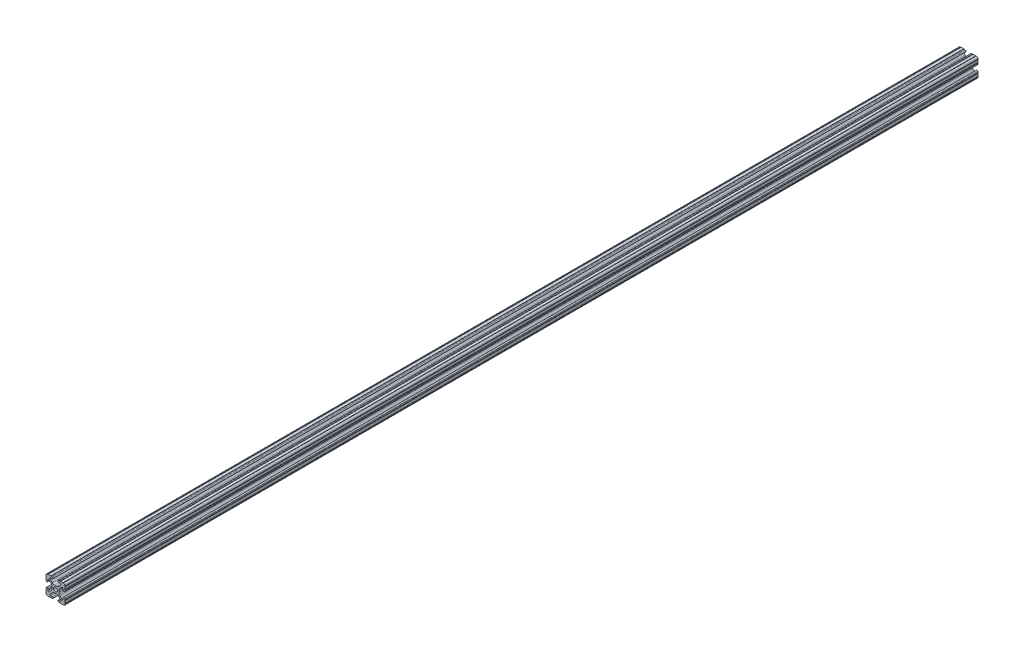
SolidWorks part; units mm, degrees
ref_plane "Front Plane" through (0, 0, 0) normal (0, 0, 1) x (1, 0, 0)
ref_plane "Top Plane" through (0, 0, 0) normal (0, 1, 0) x (1, 0, 0)
ref_plane "Right Plane" through (0, 0, 0) normal (1, 0, 0) x (0, 0, -1)
sketch "Sketch1" plane through (0, 0, 0) normal (0, 0, 1) x (1, 0, 0)
  line L0 (0, 12.7) -> (-12.7814, 12.7) construction
  line L1 (-4.5085, 0) -> (-4.5085, 2.9459)
  line L2 (-6.0437, 12.5461) -> (-10.0976, 12.6876) construction
  line L3 (-11.5616, 12.4229) -> (-4.3159, 12.1699) construction
  line L4 (-6.4364, 10.3486) -> (-6.3592, 12.5571) construction
  line L6 (-2.9459, 4.5085) -> (0, 4.5085)
  line L7 (0, 0) -> (0, 12.7) construction
  line L8 (0, 0) -> (-12.7814, 0) construction
  line L9 (0.7813, 0.7813) -> (-0.7813, -0.7813) construction
  line L10 (-2.9459, 4.5085) -> (-7.1484, 8.711)
  line L11 (-4.5085, 2.9459) -> (-8.711, 7.1484)
  line L13 (0, 0) -> (-12.7814, 12.7814) construction
  line L14 (-10.4131, 12.6987) -> (-4.3048, 12.4853)
  line L15 (-4.3048, 12.4853) -> (-4.382, 10.2769) construction
  line L16 (-4.382, 10.2769) -> (-6.4364, 10.3486)
  line L17 (-12.6987, 10.4131) -> (-12.4853, 4.3048)
  line L18 (-10.2769, 4.382) -> (-10.3486, 6.4364)
  circle A0 centre (0, 0) radius 2.6035
  arc A1 (-4.382, 10.2769) -> (-4.3048, 12.4853) centre (-4.3434, 11.3811) ccw
  arc A2 (-7.1484, 8.711) -> (-6.4364, 10.3486) centre (-6.4698, 9.3896) cw
  arc A3 (-8.711, 7.1484) -> (-10.3486, 6.4364) centre (-9.3896, 6.4698) ccw
  arc A4 (-10.2769, 4.382) -> (-12.4853, 4.3048) centre (-11.3811, 4.3434) cw
  arc A5 (-10.4131, 12.6987) -> (-12.6987, 10.4131) centre (-10.4902, 10.4902) ccw
  arc A6 (-10.4131, 12.6987) -> (-9.7821, 12.6766) centre (-10.0976, 12.6876) ccw
  arc A7 (-6.3592, 12.5571) -> (-5.7282, 12.5351) centre (-6.0437, 12.5461) ccw
  arc A8 (-12.5571, 6.3592) -> (-12.5351, 5.7282) centre (-12.5461, 6.0437) cw
  arc A9 (-12.6987, 10.4131) -> (-12.6766, 9.7821) centre (-12.6876, 10.0976) cw
  dimension "D1" = 5.207
  dimension "D5" = 14.859
  dimension "D9" = 2
  dimension "D2" = 25.4
  dimension "D12" = 0.6314
  dimension "D10" = 2.2098
  dimension "D3" = 9.017
  dimension "D4" = 9.017
  dimension "D6" = 25.4
  dimension "D7" = 6.477
  dimension "D8" = 2.2098
  dimension "D11" = 12.7
sketch "Sketch3" plane through (0, 0, 0) normal (0, 0, 1) x (1, 0, 0)
  line L0 (-2.9459, 4.5085) -> (0, 4.5085) construction
  line L1 (-2.9459, 4.5085) -> (-7.1484, 8.711) construction
  line L2 (-4.382, 10.2769) -> (-6.4364, 10.3486) construction
  line L3 (-10.4131, 12.6987) -> (-4.3048, 12.4853) construction
  line L4 (-4.5085, 0) -> (-4.5085, 2.9459) construction
  line L5 (-4.5085, 2.9459) -> (-8.711, 7.1484) construction
  line L6 (-10.2769, 4.382) -> (-10.3486, 6.4364) construction
  line L7 (-12.6987, 10.4131) -> (-12.4853, 4.3048) construction
  line L8 (-1.1153, 4.5085) -> (1.1153, 4.5085)
  line L9 (-4.2404, 5.803) -> (-7.1484, 8.711)
  line L10 (-4.382, 10.2769) -> (-6.4364, 10.3486)
  line L11 (-9.7821, 12.6766) -> (-6.3592, 12.5571)
  line L12 (-4.5085, -1.1153) -> (-4.5085, 1.1153)
  line L13 (-5.803, 4.2404) -> (-8.711, 7.1484)
  line L14 (-10.2769, 4.382) -> (-10.3486, 6.4364)
  line L15 (-12.6766, 9.7821) -> (-12.5571, 6.3592)
  line L16 (-5.7282, 12.5351) -> (-4.3048, 12.4853)
  line L17 (-12.5351, 5.7282) -> (-12.4853, 4.3048)
  line L18 (0, 0) -> (0, 12.7) construction
  line L19 (0, 0) -> (-12.7814, 0) construction
  line L20 (12.5351, 5.7282) -> (12.4853, 4.3048)
  line L21 (5.7282, 12.5351) -> (4.3048, 12.4853)
  line L22 (12.6766, 9.7821) -> (12.5571, 6.3592)
  line L23 (10.2769, 4.382) -> (10.3486, 6.4364)
  line L24 (5.803, 4.2404) -> (8.711, 7.1484)
  line L25 (4.5085, -1.1153) -> (4.5085, 1.1153)
  line L26 (9.7821, 12.6766) -> (6.3592, 12.5571)
  line L27 (4.382, 10.2769) -> (6.4364, 10.3486)
  line L28 (4.2404, 5.803) -> (7.1484, 8.711)
  line L29 (4.2404, -5.803) -> (7.1484, -8.711)
  line L30 (4.382, -10.2769) -> (6.4364, -10.3486)
  line L31 (9.7821, -12.6766) -> (6.3592, -12.5571)
  line L32 (5.803, -4.2404) -> (8.711, -7.1484)
  line L33 (10.2769, -4.382) -> (10.3486, -6.4364)
  line L34 (12.6766, -9.7821) -> (12.5571, -6.3592)
  line L35 (5.7282, -12.5351) -> (4.3048, -12.4853)
  line L36 (12.5351, -5.7282) -> (12.4853, -4.3048)
  line L37 (-12.5351, -5.7282) -> (-12.4853, -4.3048)
  line L38 (-5.7282, -12.5351) -> (-4.3048, -12.4853)
  line L39 (-12.6766, -9.7821) -> (-12.5571, -6.3592)
  line L40 (-10.2769, -4.382) -> (-10.3486, -6.4364)
  line L41 (-5.803, -4.2404) -> (-8.711, -7.1484)
  line L42 (-9.7821, -12.6766) -> (-6.3592, -12.5571)
  line L43 (-4.382, -10.2769) -> (-6.4364, -10.3486)
  line L44 (-4.2404, -5.803) -> (-7.1484, -8.711)
  line L45 (-1.1153, -4.5085) -> (1.1153, -4.5085)
  arc A0 (-10.4131, 12.6987) -> (-9.7821, 12.6766) centre (-10.0976, 12.6876) ccw construction
  arc A1 (-6.4364, 10.3486) -> (-7.1484, 8.711) centre (-6.4698, 9.3896) ccw construction
  arc A2 (-4.382, 10.2769) -> (-4.3048, 12.4853) centre (-4.3434, 11.3811) ccw construction
  arc A3 (-8.711, 7.1484) -> (-10.3486, 6.4364) centre (-9.3896, 6.4698) ccw construction
  arc A4 (-12.4853, 4.3048) -> (-10.2769, 4.382) centre (-11.3811, 4.3434) ccw construction
  arc A5 (-6.3592, 12.5571) -> (-5.7282, 12.5351) centre (-6.0437, 12.5461) ccw construction
  arc A6 (-10.4131, 12.6987) -> (-12.6987, 10.4131) centre (-10.4902, 10.4902) ccw construction
  arc A7 (-12.6766, 9.7821) -> (-12.6987, 10.4131) centre (-12.6876, 10.0976) ccw construction
  arc A8 (-12.5351, 5.7282) -> (-12.5571, 6.3592) centre (-12.5461, 6.0437) ccw construction
  arc A9 (-10.4131, 12.6987) -> (-9.7821, 12.6766) centre (-10.0976, 12.6876) ccw
  arc A10 (-6.4364, 10.3486) -> (-7.1484, 8.711) centre (-6.4698, 9.3896) ccw
  arc A11 (-4.382, 10.2769) -> (-4.3048, 12.4853) centre (-4.3434, 11.3811) ccw
  arc A12 (-8.711, 7.1484) -> (-10.3486, 6.4364) centre (-9.3896, 6.4698) ccw
  arc A13 (-12.4853, 4.3048) -> (-10.2769, 4.382) centre (-11.3811, 4.3434) ccw
  arc A14 (-6.3592, 12.5571) -> (-5.7282, 12.5351) centre (-6.0437, 12.5461) ccw
  arc A15 (-10.4131, 12.6987) -> (-12.6987, 10.4131) centre (-10.4902, 10.4902) ccw
  arc A16 (-12.6766, 9.7821) -> (-12.6987, 10.4131) centre (-12.6876, 10.0976) ccw
  arc A17 (-12.5351, 5.7282) -> (-12.5571, 6.3592) centre (-12.5461, 6.0437) ccw
  arc A18 (-1.1153, 4.5085) -> (-4.2404, 5.803) centre (-1.1153, 8.9281) cw
  arc A19 (4.5085, 1.1153) -> (5.803, 4.2404) centre (8.9281, 1.1153) cw
  arc A20 (1.1153, 4.5085) -> (4.2404, 5.803) centre (1.1153, 8.9281) ccw
  arc A21 (-4.5085, 1.1153) -> (-5.803, 4.2404) centre (-8.9281, 1.1153) ccw
  arc A22 (12.5351, 5.7282) -> (12.5571, 6.3592) centre (12.5461, 6.0437) cw
  arc A23 (12.6766, 9.7821) -> (12.6987, 10.4131) centre (12.6876, 10.0976) cw
  arc A24 (10.4131, 12.6987) -> (12.6987, 10.4131) centre (10.4902, 10.4902) cw
  arc A25 (6.3592, 12.5571) -> (5.7282, 12.5351) centre (6.0437, 12.5461) cw
  arc A26 (12.4853, 4.3048) -> (10.2769, 4.382) centre (11.3811, 4.3434) cw
  arc A27 (8.711, 7.1484) -> (10.3486, 6.4364) centre (9.3896, 6.4698) cw
  arc A28 (4.382, 10.2769) -> (4.3048, 12.4853) centre (4.3434, 11.3811) cw
  arc A29 (6.4364, 10.3486) -> (7.1484, 8.711) centre (6.4698, 9.3896) cw
  arc A30 (10.4131, 12.6987) -> (9.7821, 12.6766) centre (10.0976, 12.6876) cw
  arc A31 (10.4131, -12.6987) -> (9.7821, -12.6766) centre (10.0976, -12.6876) ccw
  arc A32 (6.4364, -10.3486) -> (7.1484, -8.711) centre (6.4698, -9.3896) ccw
  arc A33 (4.382, -10.2769) -> (4.3048, -12.4853) centre (4.3434, -11.3811) ccw
  arc A34 (8.711, -7.1484) -> (10.3486, -6.4364) centre (9.3896, -6.4698) ccw
  arc A35 (12.4853, -4.3048) -> (10.2769, -4.382) centre (11.3811, -4.3434) ccw
  arc A36 (6.3592, -12.5571) -> (5.7282, -12.5351) centre (6.0437, -12.5461) ccw
  arc A37 (10.4131, -12.6987) -> (12.6987, -10.4131) centre (10.4902, -10.4902) ccw
  arc A38 (12.6766, -9.7821) -> (12.6987, -10.4131) centre (12.6876, -10.0976) ccw
  arc A39 (12.5351, -5.7282) -> (12.5571, -6.3592) centre (12.5461, -6.0437) ccw
  arc A40 (-4.5085, -1.1153) -> (-5.803, -4.2404) centre (-8.9281, -1.1153) cw
  arc A41 (1.1153, -4.5085) -> (4.2404, -5.803) centre (1.1153, -8.9281) cw
  arc A42 (4.5085, -1.1153) -> (5.803, -4.2404) centre (8.9281, -1.1153) ccw
  arc A43 (-1.1153, -4.5085) -> (-4.2404, -5.803) centre (-1.1153, -8.9281) ccw
  arc A44 (-12.5351, -5.7282) -> (-12.5571, -6.3592) centre (-12.5461, -6.0437) cw
  arc A45 (-12.6766, -9.7821) -> (-12.6987, -10.4131) centre (-12.6876, -10.0976) cw
  arc A46 (-10.4131, -12.6987) -> (-12.6987, -10.4131) centre (-10.4902, -10.4902) cw
  arc A47 (-6.3592, -12.5571) -> (-5.7282, -12.5351) centre (-6.0437, -12.5461) cw
  arc A48 (-12.4853, -4.3048) -> (-10.2769, -4.382) centre (-11.3811, -4.3434) cw
  arc A49 (-8.711, -7.1484) -> (-10.3486, -6.4364) centre (-9.3896, -6.4698) cw
  arc A50 (-4.382, -10.2769) -> (-4.3048, -12.4853) centre (-4.3434, -11.3811) cw
  arc A51 (-6.4364, -10.3486) -> (-7.1484, -8.711) centre (-6.4698, -9.3896) cw
  arc A52 (-10.4131, -12.6987) -> (-9.7821, -12.6766) centre (-10.0976, -12.6876) cw
  circle A53 centre (0, 0) radius 2.6035 construction
  circle A54 centre (0, 0) radius 2.6035
  point P135 (4.5085, 0)
  dimension "D2" = 4.4196
extrude "Extrude1" add sketch "Sketch3" along normal mid plane 1219.2
equation "\"D10@Sketch1\" = \"D8@Sketch1\""
equation "\"D11@Sketch1\" = \"D6@Sketch1\"/2"
equation "\"D12@Sketch1\" = \"D8@Sketch1\"/3.5"
equation "\"D2@Sketch3\" = \"D8@Sketch1\"*2"
